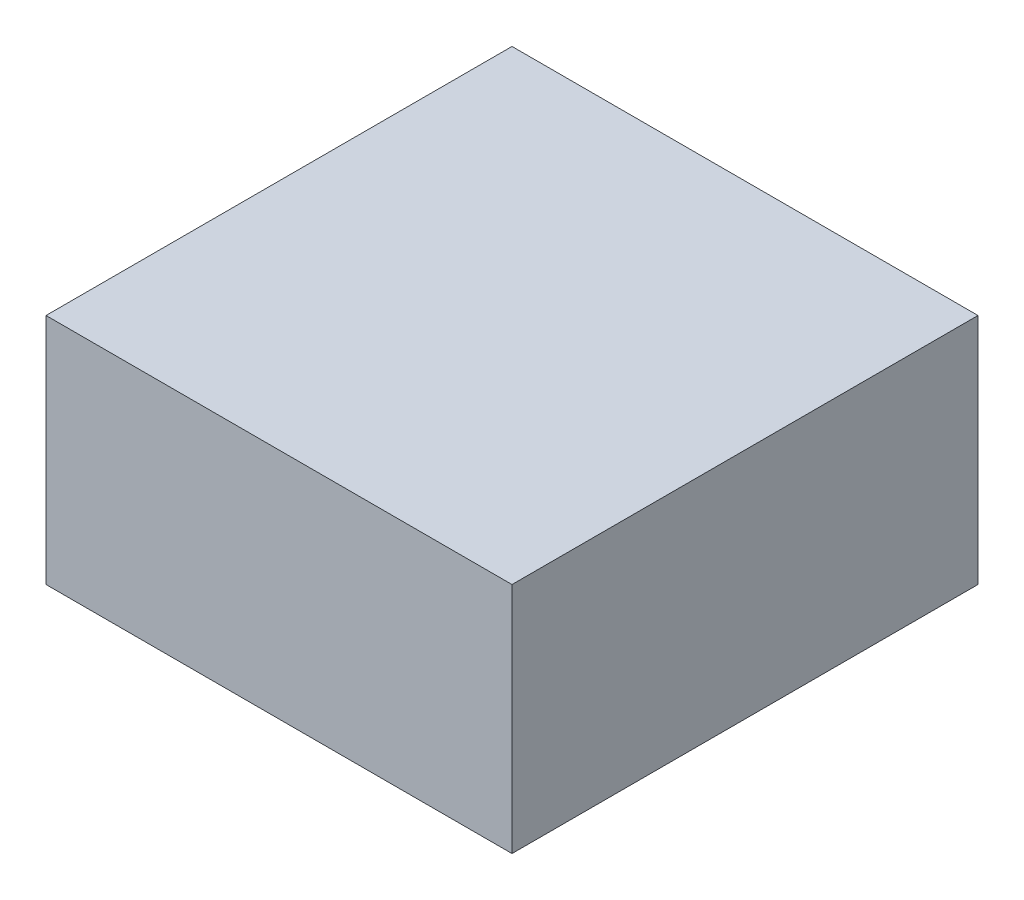
SolidWorks part; units mm, degrees
ref_plane "Front Plane" through (0, 0, 0) normal (0, 0, 1) x (1, 0, 0)
ref_plane "Top Plane" through (0, 0, 0) normal (0, 1, 0) x (1, 0, 0)
ref_plane "Right Plane" through (0, 0, 0) normal (1, 0, 0) x (0, 0, -1)
sketch "Sketch1" plane through (0, 0, 0) normal (0, 1, 0) x (1, 0, 0)
  line L1 (0, 0) -> (100, 0)
  line L2 (0, 0) -> (0, -100)
  line L3 (0, -100) -> (100, -100)
  line L4 (100, 0) -> (100, -100)
  point P5 (50, 0)
  dimension "D1" = 100
  dimension "D2" = 100
extrude "Boss-Extrude1" add sketch "Sketch1" along normal blind 50 contours L2 L1 L4 L3
sketch "Sketch3" plane through (0, 0, 0) normal (-1, 0, 0) x (0, 0, 1)
  circle A0 centre (32.8346, 32.9261) radius 9.075
extrude "Cut-Extrude1" cut sketch "Sketch3" against normal blind 50
sketch "Sketch7" plane through (0, 0, 0) normal (-1, 0, 0) x (0, 0, 1)
  text T0 "  \r\n\r\n\r\n\r\n\r\nArham <b>Khan</b>"
extrude "Cut-Extrude2" cut sketch "Sketch7" against normal blind 10
